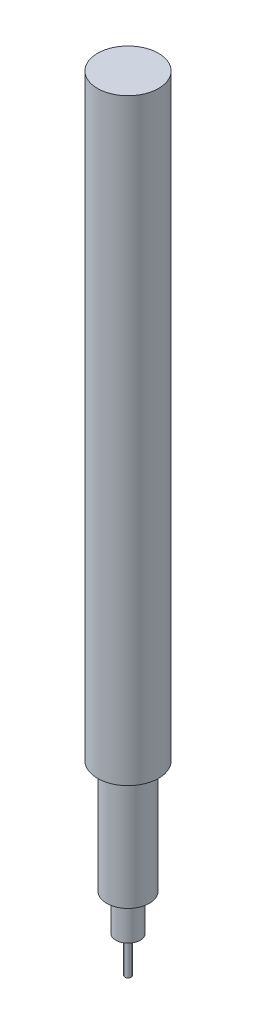
SolidWorks part; units mm, degrees
ref_plane "Plano frontal" through (0, 0, 0) normal (0, 0, 1) x (1, 0, 0)
ref_plane "Plano superior" through (0, 0, 0) normal (0, 1, 0) x (1, 0, 0)
ref_plane "Plano direito" through (0, 0, 0) normal (1, 0, 0) x (0, 0, -1)
sketch "Esboço1" plane through (0, 0, 0) normal (0, 0, 1) x (1, 0, 0)
  line L0 (0, 0) -> (0, 96.6126) construction
  line L1 (0, 0) -> (0.5, 0)
  line L2 (0.5, 0) -> (0.5, 5)
  line L3 (0.5, 5) -> (2, 6)
  line L4 (2, 6) -> (2, 12)
  line L5 (2, 12) -> (3.5, 12)
  line L6 (3.5, 12) -> (3.5, 30.5)
  line L7 (3.5, 30.5) -> (5, 30.5)
  line L8 (5, 30.5) -> (5, 128.5)
  line L9 (5, 128.5) -> (0, 128.5)
  line L10 (0, 0) -> (0, 128.5)
  point P3 (0, 128.5)
  dimension "D1" = 98
  dimension "D2" = 30.5
  dimension "D3" = 5
  dimension "D4" = 1
  dimension "D5" = 6
  dimension "D6" = 18.5
  dimension "D7" = 1
  dimension "D8" = 4
  dimension "D9" = 7
  dimension "D10" = 10
revolve "Revolução1" add sketch "Esboço1" angle 360 about L0
